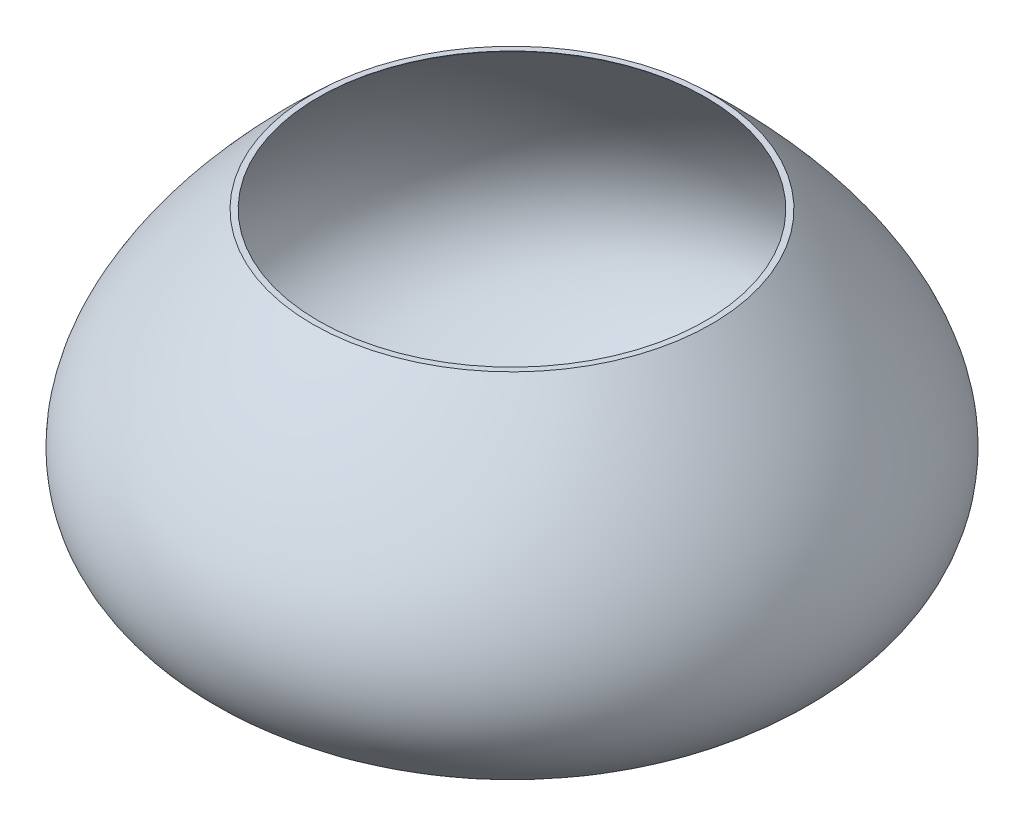
SolidWorks part; units mm, degrees
ref_plane "Front Plane" through (0, 0, 0) normal (0, 0, 1) x (1, 0, 0)
ref_plane "Top Plane" through (0, 0, 0) normal (0, 1, 0) x (1, 0, 0)
ref_plane "Right Plane" through (0, 0, 0) normal (1, 0, 0) x (0, 0, -1)
sketch "Sketch1" plane through (0, 0, 0) normal (0, 0, 1) x (1, 0, 0)
  line L0 (-50.7285, 42.6157) -> (0, 42.6157)
  line L1 (0, -55) -> (0, 55) construction
  line L2 (0, 42.6157) -> (0, -51.5678)
  line L3 (0, -51.5678) -> (-19.3962, -51.5678)
  spline S0 degree 2 poles (-50.7285, 42.6157) (-130.0281, -31.1829) (-19.3962, -51.5678) knots 0 0 0 1 1 1
revolve "Revolve1" add sketch "Sketch1" angle 360 about L2
sketch "Sketch2" plane through (0, 0, 0) normal (0, 0, 1) x (1, 0, 0)
  line L0 (-50.047, 41.8838) -> (-41.0856, 50.2288)
  line L1 (-41.0856, 50.2288) -> (0, 50.2288)
  line L2 (0, -51.8009) -> (0, 51.8009) construction
  line L3 (0, 50.2288) -> (0, -50.5844)
  line L4 (0, -50.5844) -> (-19.2147, -50.5844)
  spline S3 degree 3 poles (1957.3836, 2271.0882) (-1.6929, 76.1439) (-25.5478, 64.8915) (-51.1557, 40.8463) (-51.4317, 40.586) (-52.258, 39.8029) (-52.8064, 39.2784) (-54.4437, 37.697) (-55.5247, 36.6324) (-58.7315, 33.4043) (-60.8217, 31.2068) (-64.8736, 26.7024) (-66.8358, 24.3954) (-70.5802, 19.6481) (-72.3632, 17.2076) (-75.6639, 12.1651) (-77.1829, 9.5625) (-79.1508, 5.5205) (-79.7545, 4.1503) (-80.8286, 1.365) (-81.2992, -0.0502) (-82.0719, -2.9184) (-82.3738, -4.3716) (-82.769, -7.2985) (-82.8618, -8.7723) (-82.802, -11.7088) (-82.649, -13.1712) (-82.08, -16.0422) (-81.664, -17.4503) (-80.5825, -20.1709) (-79.9176, -21.4832) (-78.3779, -23.9869) (-77.5039, -25.1784) (-75.5943, -27.4347) (-74.5591, -28.4999) (-72.37, -30.5112) (-71.2162, -31.4575) (-67.6257, -34.1378) (-65.0632, -35.714) (-59.7599, -38.5517) (-57.0172, -39.8135) (-51.4293, -42.1038) (-48.5832, -43.132) (-42.8279, -45.0104) (-39.9183, -45.8603) (-34.0586, -47.4202) (-31.1082, -48.1301) (-26.6621, -49.1102) (-25.1766, -49.4228) (-22.9441, -49.8723) (-22.1992, -50.019) (33.2753, -60.7029) (79.4813, -51.2862) (2868.6888, -862.4889) knots -0.707499 -0.707499 -0.707499 -0.707499 0.007812 0.007812 0.015625 0.015625 0.03125 0.03125 0.0625 0.0625 0.125 0.125 0.1875 0.1875 0.25 0.25 0.3125 0.3125 0.34375 0.34375 0.375 0.375 0.40625 0.40625 0.4375 0.4375 0.46875 0.46875 0.5 0.5 0.53125 0.53125 0.5625 0.5625 0.59375 0.59375 0.625 0.625 0.6875 0.6875 0.75 0.75 0.8125 0.8125 0.875 0.875 0.9375 0.9375 0.96875 0.96875 0.984375 0.984375 2.131342 2.131342 2.131342 2.131342 only from (-50.047, 41.8838) to (-19.2147, -50.5844)
  spline S4 degree 3 poles (-50.047, 41.8838) (-50.3258, 41.6242) (-50.6023, 41.3659) (-51.1557, 40.8463) (-51.4317, 40.586) (-52.258, 39.8029) (-52.8064, 39.2784) (-54.4437, 37.697) (-55.5247, 36.6324) (-58.7315, 33.4043) (-60.8217, 31.2068) (-64.8736, 26.7024) (-66.8358, 24.3954) (-70.5802, 19.6481) (-72.3632, 17.2076) (-75.6639, 12.1651) (-77.1829, 9.5625) (-79.1508, 5.5205) (-79.7545, 4.1503) (-80.8286, 1.365) (-81.2992, -0.0502) (-82.0719, -2.9184) (-82.3738, -4.3716) (-82.769, -7.2985) (-82.8618, -8.7723) (-82.802, -11.7088) (-82.649, -13.1712) (-82.08, -16.0422) (-81.664, -17.4503) (-80.5825, -20.1709) (-79.9176, -21.4832) (-78.3779, -23.9869) (-77.5039, -25.1784) (-75.5943, -27.4347) (-74.5591, -28.4999) (-72.37, -30.5112) (-71.2162, -31.4575) (-67.6257, -34.1378) (-65.0632, -35.714) (-59.7599, -38.5517) (-57.0172, -39.8135) (-51.4293, -42.1038) (-48.5832, -43.132) (-42.8279, -45.0104) (-39.9183, -45.8603) (-34.0586, -47.4202) (-31.1082, -48.1301) (-26.6621, -49.1102) (-25.1766, -49.4228) (-22.9441, -49.8723) (-22.1992, -50.019) (-20.708, -50.3062) (-19.964, -50.4461) (-19.2147, -50.5844) knots 0 0 0 0 0.007812 0.007812 0.015625 0.015625 0.03125 0.03125 0.0625 0.0625 0.125 0.125 0.1875 0.1875 0.25 0.25 0.3125 0.3125 0.34375 0.34375 0.375 0.375 0.40625 0.40625 0.4375 0.4375 0.46875 0.46875 0.5 0.5 0.53125 0.53125 0.5625 0.5625 0.59375 0.59375 0.625 0.625 0.6875 0.6875 0.75 0.75 0.8125 0.8125 0.875 0.875 0.9375 0.9375 0.96875 0.96875 0.984375 0.984375 1 1 1 1
  dimension "D1" = 1
revolve "Cut-Revolve1" cut sketch "Sketch2" angle 360 about L3
